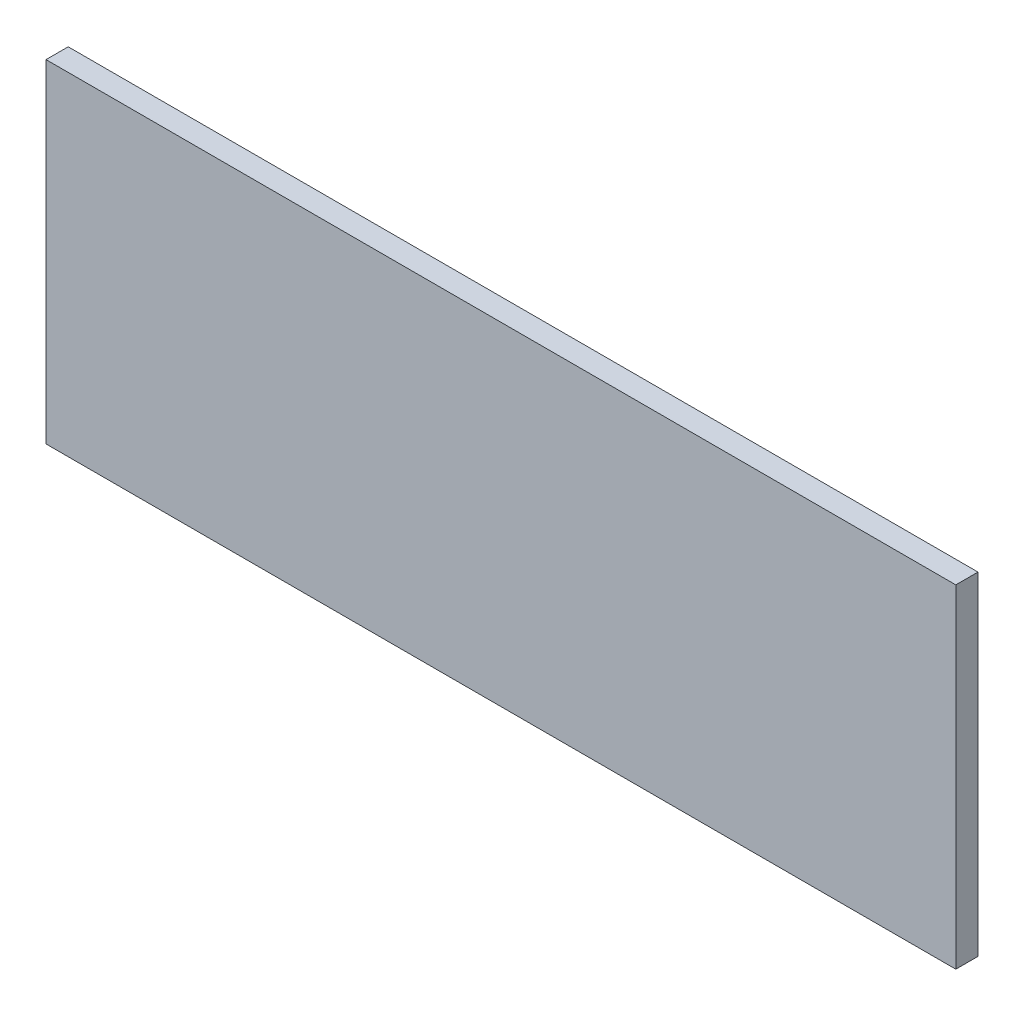
SolidWorks part; units mm, degrees
ref_plane "Front Plane" through (0, 0, 0) normal (0, 0, 1) x (1, 0, 0)
ref_plane "Top Plane" through (0, 0, 0) normal (0, 1, 0) x (1, 0, 0)
ref_plane "Right Plane" through (0, 0, 0) normal (1, 0, 0) x (0, 0, -1)
sketch "Sketch1" plane through (0, 0, 0) normal (0, 0, 1) x (1, 0, 0)
  line L1 (-82, 30) -> (82, 30)
  line L2 (-82, 30) -> (-82, -30)
  line L3 (-82, -30) -> (82, -30)
  line L4 (82, 30) -> (82, -30)
  line L5 (-82, 30) -> (82, -30) construction
  line L6 (-82, -30) -> (82, 30) construction
  point P0 (0, 0)
  dimension "D1" = 164
  dimension "D2" = 60
extrude "Boss-Extrude1" add sketch "Sketch1" against normal blind 4
